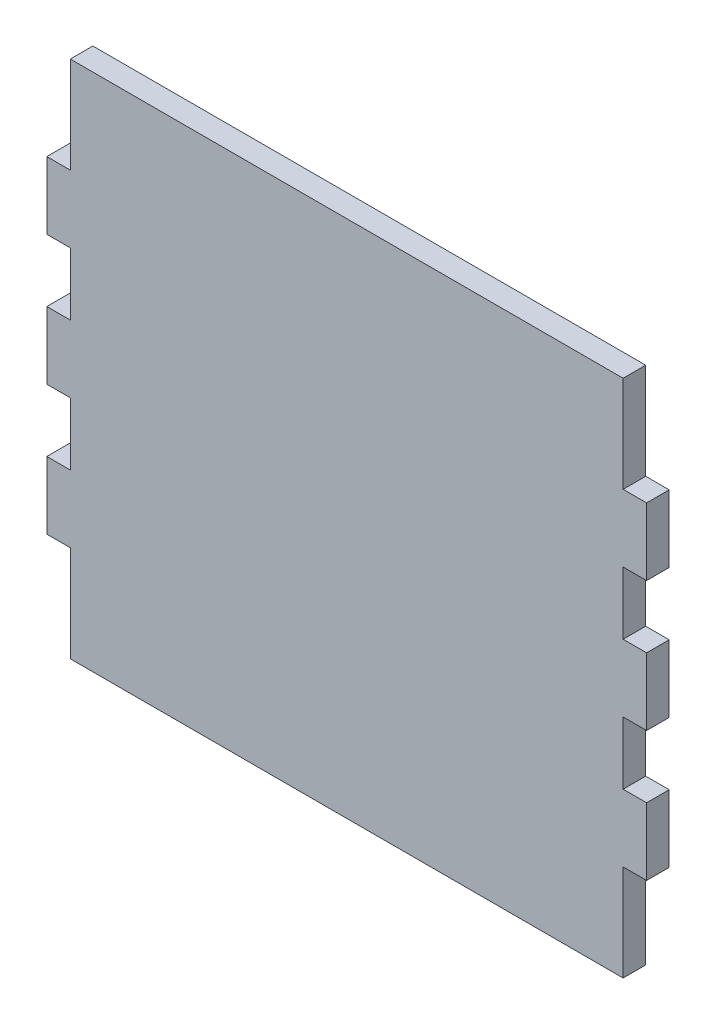
SolidWorks part; units mm, degrees
ref_plane "Front Plane" through (0, 0, 0) normal (0, 0, 1) x (1, 0, 0)
ref_plane "Top Plane" through (0, 0, 0) normal (0, 1, 0) x (1, 0, 0)
ref_plane "Right Plane" through (0, 0, 0) normal (1, 0, 0) x (0, 0, -1)
sketch "Sketch1" plane through (0, 0, 0) normal (0, 0, 1) x (1, 0, 0)
  line L0 (0, 0) -> (-84.328, 0) construction
  line L1 (77.724, 73.025) -> (-77.724, 73.025)
  line L2 (77.724, 73.025) -> (77.724, 45.974)
  line L3 (77.724, -73.025) -> (-77.724, -73.025)
  line L4 (-77.724, 73.025) -> (-77.724, 45.974)
  line L5 (77.724, 73.025) -> (-77.724, -73.025) construction
  line L6 (77.724, -73.025) -> (-77.724, 73.025) construction
  line L7 (-77.724, 9.4615) -> (-84.328, 9.4615)
  line L9 (-77.724, -9.4615) -> (-84.328, -9.4615)
  line L10 (-84.328, 9.4615) -> (-84.328, -9.4615)
  line L11 (-77.724, -27.051) -> (-84.328, -27.051)
  line L13 (-77.724, -45.974) -> (-84.328, -45.974)
  line L14 (-84.328, -27.051) -> (-84.328, -45.974)
  line L15 (-77.724, 45.974) -> (-84.328, 45.974)
  line L17 (-77.724, 27.051) -> (-84.328, 27.051)
  line L18 (-84.328, 45.974) -> (-84.328, 27.051)
  line L19 (-77.724, 73.025) -> (-77.724, 45.974) construction
  line L20 (-84.328, 36.5125) -> (0, 36.5125) construction
  line L21 (-84.328, -36.5125) -> (0, -36.5125) construction
  line L22 (-42.164, -36.5125) -> (-42.164, 0) construction
  line L23 (-42.164, -36.5125) -> (-42.164, -73.025) construction
  line L24 (-77.724, 27.051) -> (-77.724, 9.4615)
  line L25 (-77.724, -9.4615) -> (-77.724, -27.051)
  line L26 (-77.724, -45.974) -> (-77.724, -73.025)
  line L27 (0, 73.025) -> (0, -73.025) construction
  line L28 (84.328, -45.974) -> (84.328, -68.2943) construction
  line L29 (84.328, -9.4615) -> (84.328, -27.051) construction
  line L30 (84.328, 27.051) -> (84.328, 9.4615) construction
  line L31 (84.328, 68.2943) -> (84.328, 45.974) construction
  line L32 (77.724, 73.025) -> (77.724, 45.974) construction
  line L33 (77.724, -45.974) -> (77.724, -73.025)
  line L34 (77.724, -9.4615) -> (77.724, -27.051)
  line L35 (77.724, 27.051) -> (77.724, 9.4615)
  line L36 (84.328, 45.974) -> (84.328, 27.051)
  line L37 (77.724, 27.051) -> (84.328, 27.051)
  line L38 (77.724, 45.974) -> (84.328, 45.974)
  line L39 (84.328, -27.051) -> (84.328, -45.974)
  line L40 (77.724, -45.974) -> (84.328, -45.974)
  line L41 (77.724, -27.051) -> (84.328, -27.051)
  line L42 (84.328, 9.4615) -> (84.328, -9.4615)
  line L43 (77.724, -9.4615) -> (84.328, -9.4615)
  line L44 (77.724, 9.4615) -> (84.328, 9.4615)
  line L45 (-42.164, 73.025) -> (-42.164, 36.5125) construction
  line L46 (-42.164, 36.5125) -> (-42.164, 0) construction
  point P0 (0, 0)
  dimension "D1" = 155.448
  dimension "D2" = 146.05
  dimension "D3" = 18.923
  dimension "D4" = 6.604
extrude "Boss-Extrude1" add sketch "Sketch1" along normal mid plane 6.35
